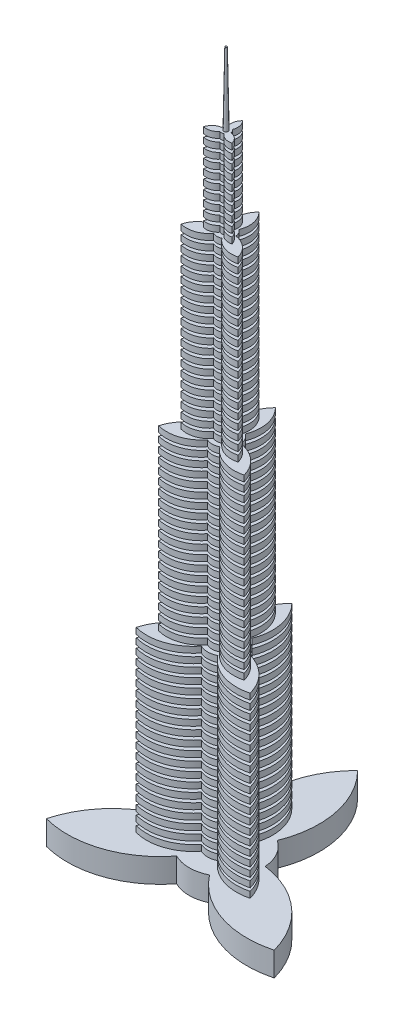
SolidWorks part; units mm, degrees
ref_plane "Front Plane" through (0, 0, 0) normal (0, 0, 1) x (1, 0, 0)
ref_plane "Top Plane" through (0, 0, 0) normal (0, 1, 0) x (1, 0, 0)
ref_plane "Right Plane" through (0, 0, 0) normal (1, 0, 0) x (0, 0, -1)
sketch "Sketch1" plane through (0, 0, 0) normal (0, 1, 0) x (1, 0, 0)
  line L0 (0, 0) -> (0, 109.2355) construction
  arc A0 (-13.632, -27.4214) -> (13.632, -27.4214) centre (0, 0) ccw
  arc A1 (-16.9316, 25.5164) -> (0, 109.2355) centre (54.6178, 54.6178) cw
  arc A2 (16.9316, 25.5164) -> (0, 109.2355) centre (-54.6178, 54.6178) ccw
  arc A3 (30.5636, 1.905) -> (94.6008, -54.6178) centre (19.9915, -74.6093) cw
  arc A4 (13.632, -27.4214) -> (94.6008, -54.6178) centre (74.6093, 19.9915) ccw
  arc A5 (-13.632, -27.4214) -> (-94.6008, -54.6178) centre (-74.6093, 19.9915) cw
  arc A6 (-30.5636, 1.905) -> (-94.6008, -54.6178) centre (-19.9915, -74.6093) ccw
  arc A7 (30.5636, 1.905) -> (16.9316, 25.5164) centre (0, 0) ccw
  arc A8 (-16.9316, 25.5164) -> (-30.5636, 1.905) centre (0, 0) ccw
  point P15 (0, 0)
  dimension "D1" = 3
extrude "Boss-Extrude1" add sketch "Sketch1" along normal blind 10
pattern_linear "LPattern1" count 20 spacing 15 along (0, 1, 0) of bodies 101
sketch "Sketch2" plane through (0, 295, 0) normal (0, 1, 0) x (1, 0, 0)
  arc A18 (10.224, -20.566) -> (70.9506, -40.9633) centre (55.9569, 14.9936) ccw
  arc A19 (70.9506, -40.9633) -> (22.9227, 1.4287) centre (14.9936, -55.9569) ccw
  arc A20 (22.9227, 1.4287) -> (12.6987, 19.1373) centre (0, 0) ccw
  arc A21 (12.6987, 19.1373) -> (0, 81.9267) centre (-40.9633, 40.9633) ccw
  arc A22 (0, 81.9267) -> (-12.6987, 19.1373) centre (40.9633, 40.9633) ccw
  arc A23 (-12.6987, 19.1373) -> (-22.9227, 1.4287) centre (0, 0) ccw
  arc A24 (-22.9227, 1.4287) -> (-70.9506, -40.9633) centre (-14.9936, -55.9569) ccw
  arc A25 (-70.9506, -40.9633) -> (-10.224, -20.566) centre (-55.9569, 14.9936) ccw
  arc A26 (-10.224, -20.566) -> (10.224, -20.566) centre (0, 0) ccw
extrude "Boss-Extrude2" add sketch "Sketch2" along normal blind 10
pattern_linear "LPattern2" count 20 spacing 15 along (0, 1, 0) of "Boss-Extrude2"
sketch "Sketch3" plane through (0, 590, 0) normal (0, 1, 0) x (1, 0, 0)
  arc A18 (6.816, -13.7107) -> (47.3004, -27.3089) centre (37.3046, 9.9957) ccw
  arc A19 (47.3004, -27.3089) -> (15.2818, 0.9525) centre (9.9957, -37.3046) ccw
  arc A20 (15.2818, 0.9525) -> (8.4658, 12.7582) centre (0, 0) ccw
  arc A21 (8.4658, 12.7582) -> (0, 54.6178) centre (-27.3089, 27.3089) ccw
  arc A22 (0, 54.6178) -> (-8.4658, 12.7582) centre (27.3089, 27.3089) ccw
  arc A23 (-8.4658, 12.7582) -> (-15.2818, 0.9525) centre (0, 0) ccw
  arc A24 (-15.2818, 0.9525) -> (-47.3004, -27.3089) centre (-9.9957, -37.3046) ccw
  arc A25 (-47.3004, -27.3089) -> (-6.816, -13.7107) centre (-37.3046, 9.9957) ccw
  arc A26 (-6.816, -13.7107) -> (6.816, -13.7107) centre (0, 0) ccw
extrude "Boss-Extrude3" add sketch "Sketch3" along normal blind 10
pattern_linear "LPattern3" count 20 spacing 15 along (0, 1, 0) of "Boss-Extrude3"
sketch "Sketch4" plane through (0, 885, 0) normal (0, 1, 0) x (1, 0, 0)
  arc A18 (3.408, -6.8553) -> (23.6502, -13.6544) centre (18.6523, 4.9979) ccw
  arc A19 (23.6502, -13.6544) -> (7.6409, 0.4762) centre (4.9979, -18.6523) ccw
  arc A20 (7.6409, 0.4762) -> (4.2329, 6.3791) centre (0, 0) ccw
  arc A21 (4.2329, 6.3791) -> (0, 27.3089) centre (-13.6544, 13.6544) ccw
  arc A22 (0, 27.3089) -> (-4.2329, 6.3791) centre (13.6544, 13.6544) ccw
  arc A23 (-4.2329, 6.3791) -> (-7.6409, 0.4762) centre (0, 0) ccw
  arc A24 (-7.6409, 0.4762) -> (-23.6502, -13.6544) centre (-4.9979, -18.6523) ccw
  arc A25 (-23.6502, -13.6544) -> (-3.408, -6.8553) centre (-18.6523, 4.9979) ccw
  arc A26 (-3.408, -6.8553) -> (3.408, -6.8553) centre (0, 0) ccw
extrude "Boss-Extrude4" add sketch "Sketch4" along normal blind 10
pattern_linear "LPattern4" count 10 spacing 15 along (0, 1, 0) of "Boss-Extrude4"
sketch "Sketch5" plane through (0, 1030, 0) normal (0, 1, 0) x (1, 0, 0)
  circle A0 centre (0, 0) radius 3.6305
extrude "Boss-Extrude5" add sketch "Sketch5" along normal blind 120 draft 1
sketch "Sketch6" plane through (0, 0, 0) normal (0, -1, 0) x (1, 0, 0)
  arc A18 (189.2015, 109.2355) -> (27.2641, 54.8428) centre (149.2185, -39.983) ccw
  arc A19 (27.2641, 54.8428) -> (-27.2641, 54.8428) centre (0, 0) ccw
  arc A20 (-27.2641, 54.8428) -> (-189.2015, 109.2355) centre (-149.2185, -39.983) ccw
  arc A21 (-189.2015, 109.2355) -> (-61.1273, -3.81) centre (-39.983, 149.2185) ccw
  arc A22 (-61.1273, -3.81) -> (-33.8632, -51.0328) centre (0, 0) ccw
  arc A23 (-33.8632, -51.0328) -> (0, -218.4711) centre (109.2355, -109.2355) ccw
  arc A24 (0, -218.4711) -> (33.8632, -51.0328) centre (-109.2355, -109.2355) ccw
  arc A25 (33.8632, -51.0328) -> (61.1273, -3.81) centre (0, 0) ccw
  arc A26 (61.1273, -3.81) -> (189.2015, 109.2355) centre (39.983, 149.2185) ccw
extrude "Boss-Extrude6" add sketch "Sketch6" along normal blind 40
